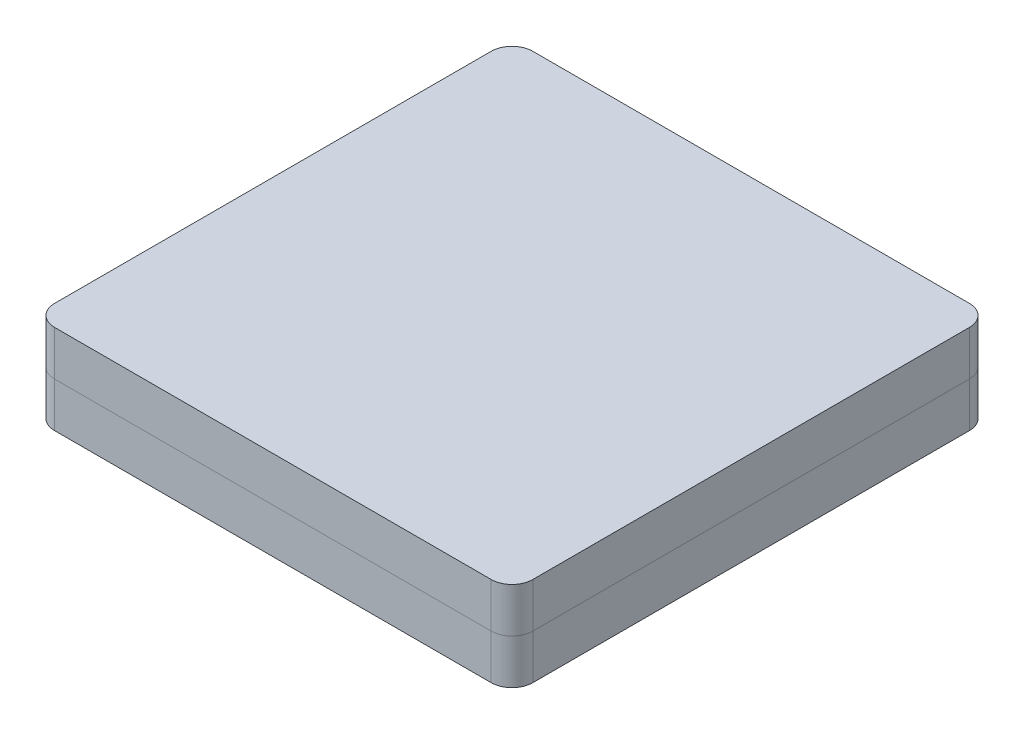
SolidWorks part; units mm, degrees
ref_plane "Front Plane" through (0, 0, 0) normal (0, 0, 1) x (1, 0, 0)
ref_plane "Top Plane" through (0, 0, 0) normal (0, 1, 0) x (1, 0, 0)
ref_plane "Right Plane" through (0, 0, 0) normal (1, 0, 0) x (0, 0, -1)
sketch "Sketch1" plane through (0, 0, 0) normal (0, 1, 0) x (1, 0, 0)
  line L1 (-10.5, -11.5) -> (10.5, -11.5)
  line L2 (-11.5, -10.5) -> (-11.5, 10.5)
  line L3 (-10.5, 11.5) -> (10.5, 11.5)
  line L4 (11.5, -10.5) -> (11.5, 10.5)
  line L5 (-11.5, -11.5) -> (11.5, 11.5) construction
  line L6 (-11.5, 11.5) -> (11.5, -11.5) construction
  arc A0 (-10.5, -11.5) -> (-11.5, -10.5) centre (-10.5, -10.5) cw
  arc A1 (10.5, -11.5) -> (11.5, -10.5) centre (10.5, -10.5) ccw
  arc A2 (10.5, 11.5) -> (11.5, 10.5) centre (10.5, 10.5) cw
  arc A3 (-11.5, 10.5) -> (-10.5, 11.5) centre (-10.5, 10.5) cw
  point P0 (0, 0)
  dimension "D2" = 1
  dimension "D1" = 23
extrude "Boss-Extrude1" add sketch "Sketch1" along normal blind 4.3
ref_plane "Plane1" through (0, 2.15, 0) normal (0, 1, 0) x (1, 0, 0)
split "Split1" trim tools "Plane1" bodies to split 101 resulting bodies 102 103
